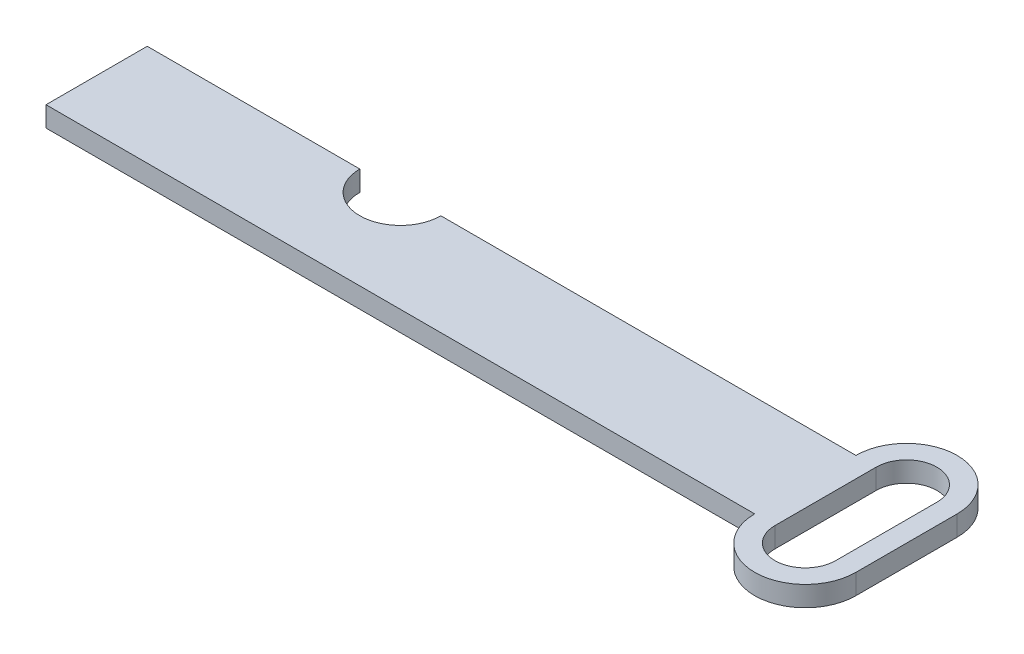
SolidWorks part; units mm, degrees
ref_plane "Front Plane" through (0, 0, 0) normal (0, 0, 1) x (1, 0, 0)
ref_plane "Top Plane" through (0, 0, 0) normal (0, 1, 0) x (1, 0, 0)
ref_plane "Right Plane" through (0, 0, 0) normal (1, 0, 0) x (0, 0, -1)
sketch "Sketch1" plane through (0, 0, 0) normal (0, 1, 0) x (1, 0, 0)
  line L0 (0, 0) -> (0, 10)
  line L1 (0, 10) -> (70, 10)
  line L2 (70, 10) -> (70, 0)
  line L3 (70, 0) -> (0, 0)
  circle A0 centre (25, 10) radius 4
  dimension "D4" = 8
  dimension "D1" = 70
  dimension "D2" = 10
  dimension "D3" = 25
extrude "Boss-Extrude1" add sketch "Sketch1" along normal blind 2 contours A0 L1 L0 L3 L2
sketch "Sketch2" plane through (0, 2, 0) normal (0, 1, 0) x (1, 0, 0)
  line L0 (75, 10) -> (75, 0) construction
  line L1 (80, 10) -> (80, 0)
  line L2 (70, 10) -> (70, 0)
  line L4 (70, 10) -> (70, 0) construction
  arc A0 (80, 10) -> (70, 10) centre (75, 10) ccw
  arc A1 (70, 0) -> (80, 0) centre (75, 0) ccw
  point P2 (75, 5)
  point P7 (74.2636, 0)
  point P8 (74.5711, 10)
  point P9 (74.4686, 0)
  point P11 (78.876, -0.5506)
  point P12 (78.9272, 10)
  point P13 (76.5185, -0.6019)
  point P14 (0, 0)
  point P15 (79.3884, 10)
  point P16 (79.3884, 0)
  point P18 (75, 15)
  point P19 (75, -5)
  dimension "D1" = 20
extrude "Boss-Extrude2" add sketch "Sketch2" against normal up to surface (2 mm away) up to face at (31.6667, 0, -6)
sketch "Sketch3" plane through (0, 2, 0) normal (0, 1, 0) x (1, 0, 0)
  line L0 (75, 10) -> (75, 0) construction
  line L1 (78, 10) -> (78, 0)
  line L2 (72, 10) -> (72, 0)
  line L3 (80, 0) -> (80, 10) construction
  line L4 (75, 15) -> (75, -5) construction
  arc A0 (78, 10) -> (72, 10) centre (75, 10) ccw
  arc A1 (72, 0) -> (78, 0) centre (75, 0) ccw
  arc A2 (80, 10) -> (70, 10) centre (75, 10) ccw construction
  arc A3 (70, 0) -> (80, 0) centre (75, 0) ccw construction
  point P2 (75, 5)
  point P7 (75, 5)
  point P12 (75, 13)
  dimension "D1" = 2
  dimension "D2" = 2
extrude "Cut-Extrude1" cut sketch "Sketch3" against normal up to surface (2 mm away) up to face at (43.75, 0, -5.75)
